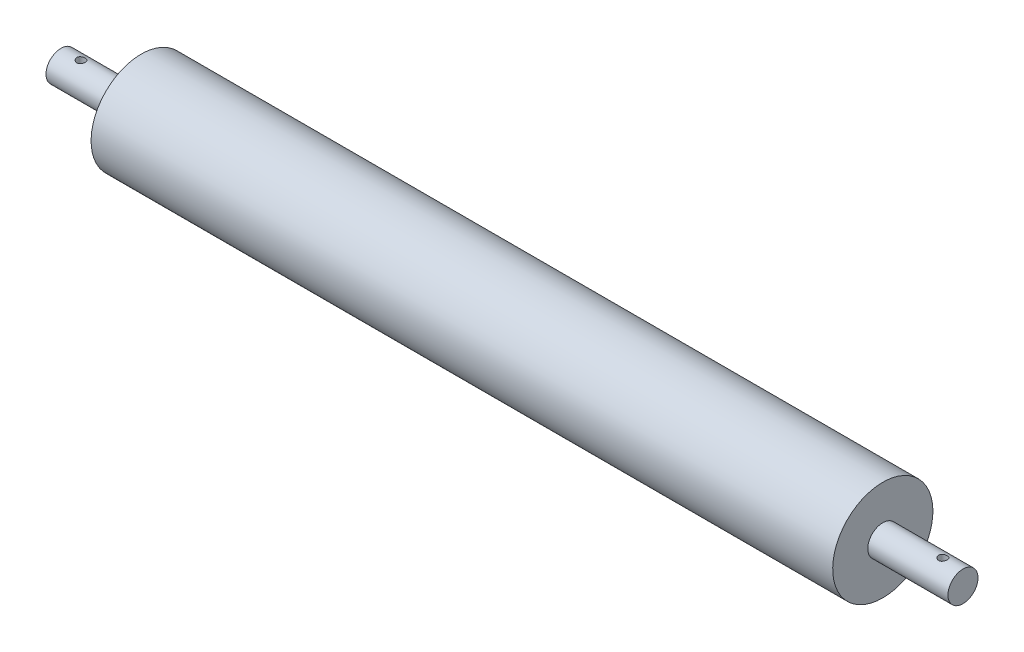
SolidWorks part; units mm, degrees
ref_plane "前视基准面" through (0, 0, 0) normal (0, 0, 1) x (1, 0, 0)
ref_plane "上视基准面" through (0, 0, 0) normal (0, 1, 0) x (1, 0, 0)
ref_plane "右视基准面" through (0, 0, 0) normal (1, 0, 0) x (0, 0, -1)
sketch "草图1" plane through (0, 0, 0) normal (0, 0, 1) x (1, 0, 0)
  line L0 (-230.7094, 0) -> (459.7941, 0) construction
  line L1 (0, 215.5466) -> (0, -189.8195) construction
  line L2 (-185, 25) -> (185, 25)
  line L8 (-185, 25) -> (-185, 7.5)
  line L9 (-225, 0) -> (225, 0)
  line L10 (-225, 0) -> (-225, 7.5)
  line L11 (-225, 7.5) -> (-185, 7.5)
  line L14 (225, 0) -> (225, 7.5)
  line L15 (225, 7.5) -> (185, 7.5)
  line L16 (185, 25) -> (185, 7.5)
  point P3 (-185, 16.25)
  point P17 (0, 25)
  dimension "D1" = 7.5
  dimension "D2" = 40
  dimension "D3" = 25
  dimension "D4" = 370
revolve "旋转1" add sketch "草图1" angle 360 about L9
ref_plane "基准面1" through (0, -7.5, 0) normal (0, -1, 0) x (-1, 0, 0)
hole_wizard "M5 螺纹孔1" positions "草图2" profile "草图3" tap size "M5" standard "GB"
sketch "草图2" plane through (0, -7.5, 0) normal (0, -1, 0) x (-1, 0, 0)
  line L0 (225, -7.5) -> (225, 7.5) construction
  line L1 (225, 0) -> (317.0408, 0) construction
  point P2 (215, 0)
  dimension "D1" = 10
  dimension "D2" = 0
sketch "草图3" plane through (-215, -7.5, 0) normal (1, 0, 0) x (0, 0, -1)
  line L0 (0, 0) -> (0, 51.2618)
  line L1 (0, 51.2618) -> (2.1, 50)
  line L2 (2.1, 50) -> (2.1, 0)
  line L5 (2.1, 0) -> (0, 0)
  line L10 (0, 51.2618) -> (-2.1, 50) construction
  line L11 (0, -6.35) -> (0, 107.95) construction
  dimension "螺纹孔钻头直径" = 4.2
  dimension "螺纹孔钻头深度" = 50
  dimension "导头角度" = 118
cosmetic thread "孔螺蚊线1"
mirror "镜向1" about plane through (0, 0, 0) normal (1, 0, 0) of "M5 螺纹孔1"
cosmetic thread "孔螺蚊线2" parameters "D1"=7.95, "D2"=5
